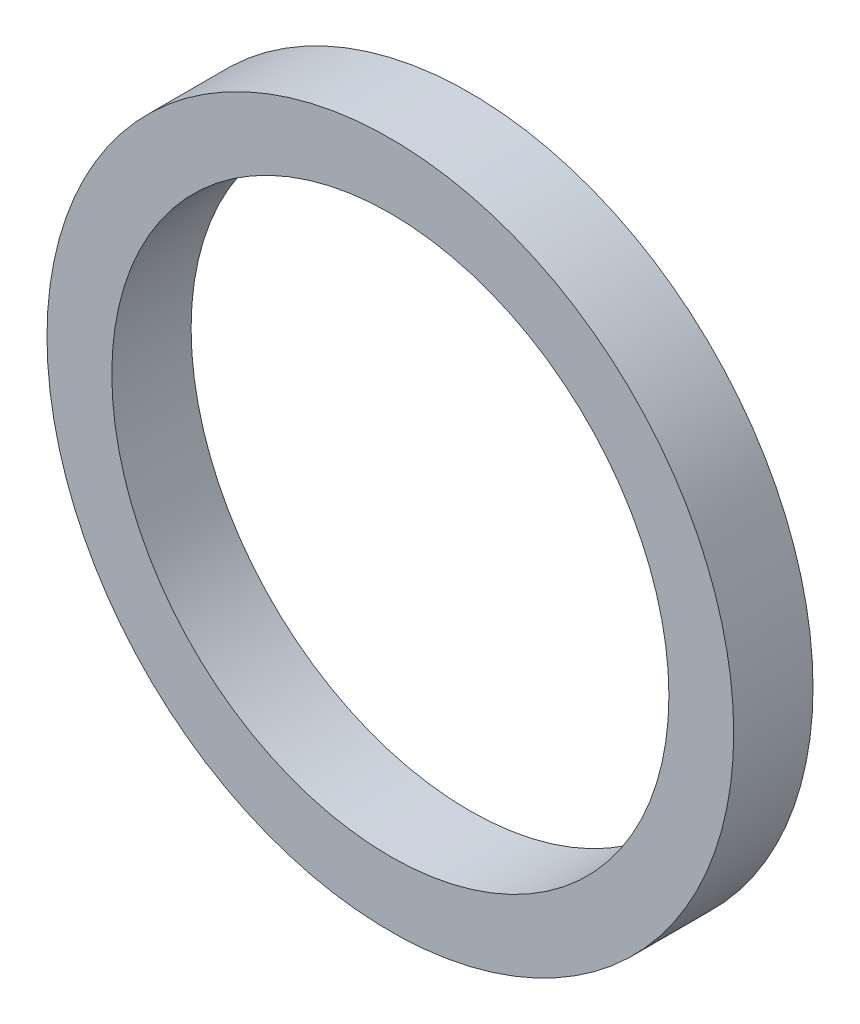
SolidWorks part; units mm, degrees
ref_plane "Front Plane" through (0, 0, 0) normal (0, 0, 1) x (1, 0, 0)
ref_plane "Top Plane" through (0, 0, 0) normal (0, 1, 0) x (1, 0, 0)
ref_plane "Right Plane" through (0, 0, 0) normal (1, 0, 0) x (0, 0, -1)
sketch "Sketch1" plane through (0, 0, 0) normal (0, 0, 1) x (1, 0, 0)
  circle A0 centre (0, 0) radius 32.9999
extrude "Boss-Extrude1" add sketch "Sketch1" along normal blind 7.62
sketch "Sketch2" plane through (0, 0, 7.62) normal (0, 0, 1) x (1, 0, 0)
  circle A0 centre (0, 0) radius 26.7701
extrude "Cut-Extrude1" cut sketch "Sketch2" against normal blind 7.62
sketch "Sketch3" plane through (0, 0, 0) normal (0, 0, -1) x (-1, 0, 0)
  text T0 "Meng Hetang\r\nZhou Jiuliang"
